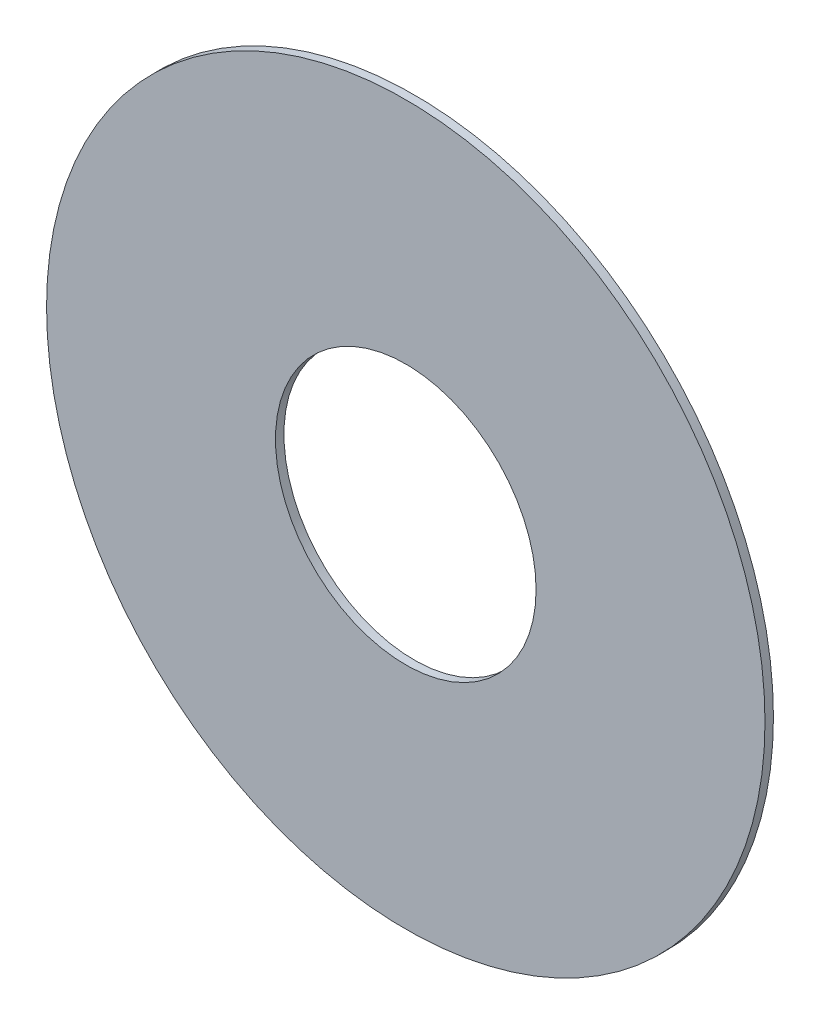
SolidWorks part; units mm, degrees
ref_plane "Front" through (0, 0, 0) normal (0, 0, 1) x (1, 0, 0)
ref_plane "Top" through (0, 0, 0) normal (0, 1, 0) x (1, 0, 0)
ref_plane "Right" through (0, 0, 0) normal (1, 0, 0) x (0, 0, -1)
sketch "Sketch1" plane through (0, 0, 0) normal (0, 0, 1) x (1, 0, 0)
  circle A0 centre (0, 0) radius 9.25
  circle A1 centre (0, 0) radius 25.5
  dimension "D1" = 18.5
  dimension "D2" = 51
extrude "Boss-Extrude1" add sketch "Sketch1" along normal blind 0.6
